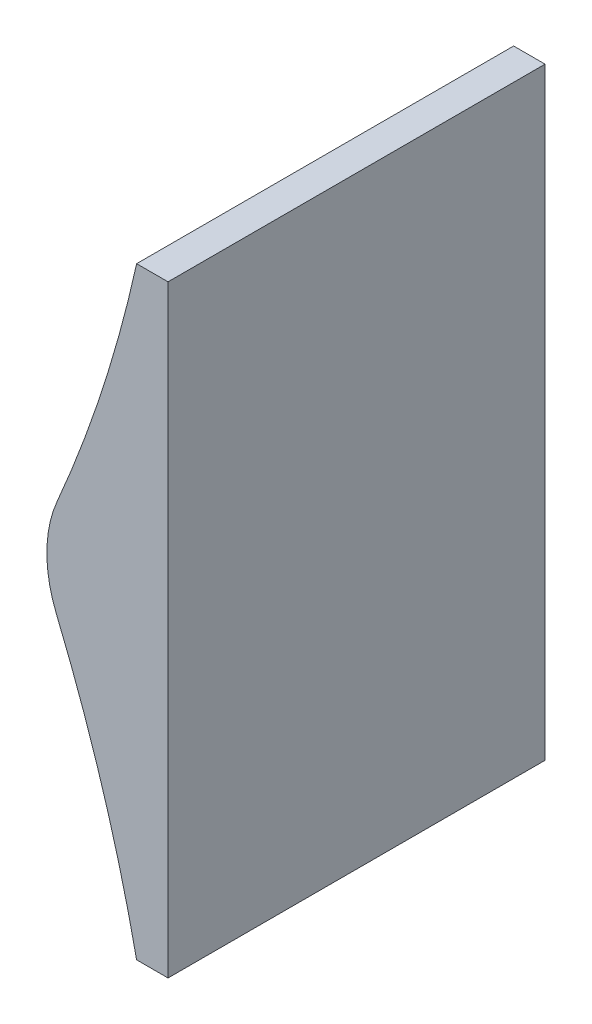
SolidWorks part; units mm, degrees
ref_plane "Front Plane" through (0, 0, 0) normal (0, 0, 1) x (1, 0, 0)
ref_plane "Top Plane" through (0, 0, 0) normal (0, 1, 0) x (1, 0, 0)
ref_plane "Right Plane" through (0, 0, 0) normal (1, 0, 0) x (0, 0, -1)
sketch "Sketch1" plane through (0, 0, 0) normal (0, 0, 1) x (1, 0, 0)
  line L0 (487.3625, 481.3783) -> (487.3625, 359.5223)
  line L1 (487.3625, 539.75) -> (487.3625, 304.8) construction
  line L2 (487.3625, 481.3783) -> (481.0125, 481.3783)
  line L3 (487.3625, 359.5223) -> (481.0125, 359.5223)
  arc A0 (481.0125, 359.5223) -> (464.802, 411.9654) centre (190.5, 298.45) ccw
  arc A1 (481.0125, 481.3783) -> (464.9672, 431.7804) centre (215.9, 539.75) cw
  circle A2 centre (215.9, 539.75) radius 266.7 construction
  circle A3 centre (190.5, 298.45) radius 292.1 construction
  arc A4 (464.9672, 431.7804) -> (464.802, 411.9654) centre (488.2717, 421.678) ccw
  dimension "D3" = 25.4
  dimension "D1" = 6.35
  dimension "D2" = 6.35
extrude "Boss-Extrude1" add sketch "Sketch1" along normal mid plane 76.2 contours A4 A0 L3 L0 L2 A1
sketch "Sketch2" plane through (487.3625, 0, 0) normal (1, 0, 0) x (0, 0, -1)
  line L0 (-38.1, 481.3783) -> (-38.1, 359.5223) construction
  line L1 (-38.1, 325.2003) -> (38.1, 325.2003)
  line L2 (-38.1, 325.2003) -> (-38.1, 515.7003)
  line L3 (-38.1, 515.7003) -> (38.1, 515.7003)
  line L4 (38.1, 325.2003) -> (38.1, 515.7003)
  line L5 (38.1, 481.3783) -> (38.1, 359.5223) construction
  line L6 (-38.1, 515.7003) -> (38.1, 481.3783) construction
  line L7 (-38.1, 325.2003) -> (38.1, 359.5223) construction
  dimension "D1" = 190.5
